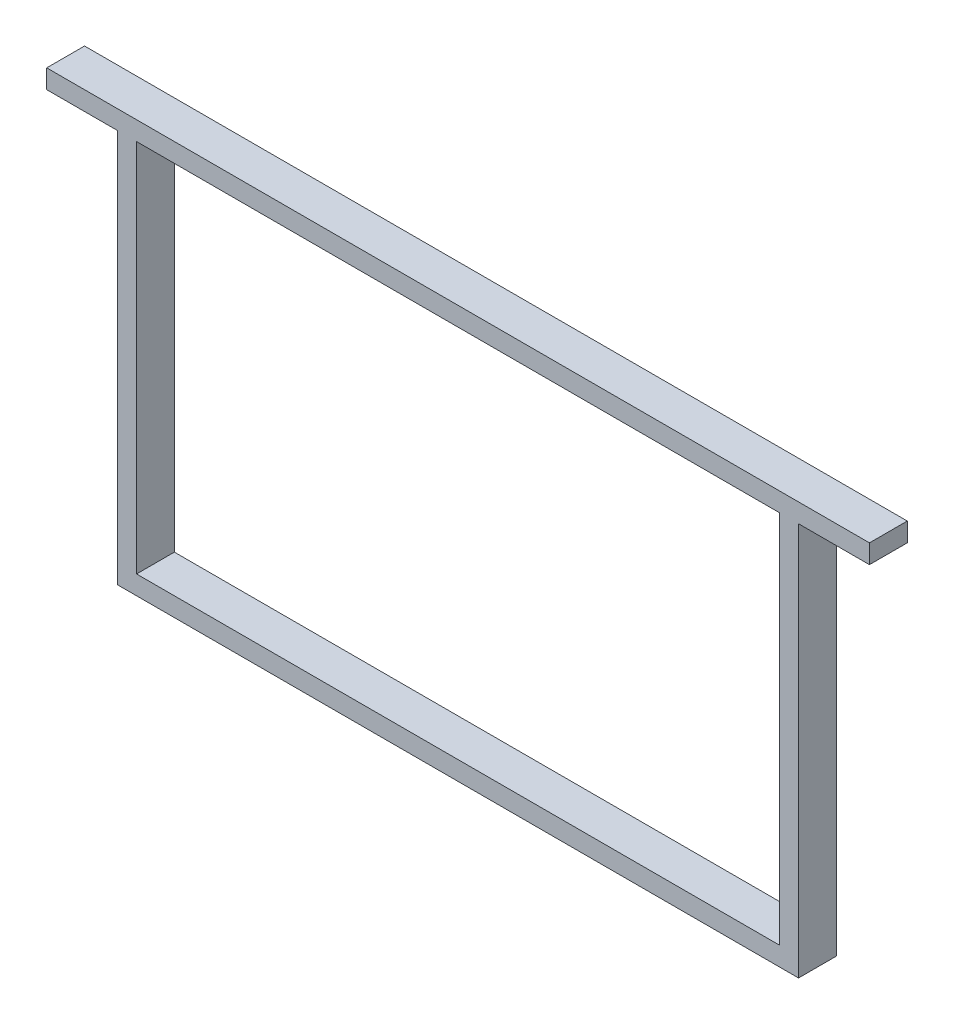
SolidWorks part; units mm, degrees
ref_plane "Front Plane" through (0, 0, 0) normal (0, 0, 1) x (1, 0, 0)
ref_plane "Top Plane" through (0, 0, 0) normal (0, 1, 0) x (1, 0, 0)
ref_plane "Right Plane" through (0, 0, 0) normal (1, 0, 0) x (0, 0, -1)
sketch "Sketch1" plane through (0, 0, 0) normal (0, 0, 1) x (1, 0, 0)
  line L0 (-180, -109) -> (-180, 109)
  line L1 (-170, -99) -> (170, -99)
  line L2 (-170, -99) -> (-170, 99)
  line L3 (-170, 99) -> (170, 99)
  line L4 (170, -99) -> (170, 99)
  line L5 (-170, -99) -> (170, 99) construction
  line L6 (-170, 99) -> (170, -99) construction
  line L7 (-180, 109) -> (180, 109)
  line L8 (180, -109) -> (180, 109)
  line L9 (-180, -109) -> (180, -109)
  line L11 (180, 109) -> (217.5, 109)
  line L12 (180, 109) -> (180, 99)
  line L13 (180, 99) -> (217.5, 99)
  line L14 (217.5, 109) -> (217.5, 99)
  line L15 (-180, 109) -> (-217.5, 109)
  line L16 (-180, 109) -> (-180, 99)
  line L17 (-180, 99) -> (-217.5, 99)
  line L18 (-217.5, 109) -> (-217.5, 99)
  point P0 (0, 0)
  point P16 (-198.75, 99)
  point P17 (-217.5, 104)
  dimension "D1" = 340
  dimension "D2" = 360
  dimension "D3" = 218
  dimension "D4" = 37.5
  dimension "D5" = 198
  dimension "D6" = 10
  dimension "D7" = 435
extrude "Boss-Extrude1" add sketch "Sketch1" along normal blind 20 contours L0 L9 L8 L7 L4 L1 L2 L3 | L15 L18 L17 L0 | L14 L11 L8 L13
